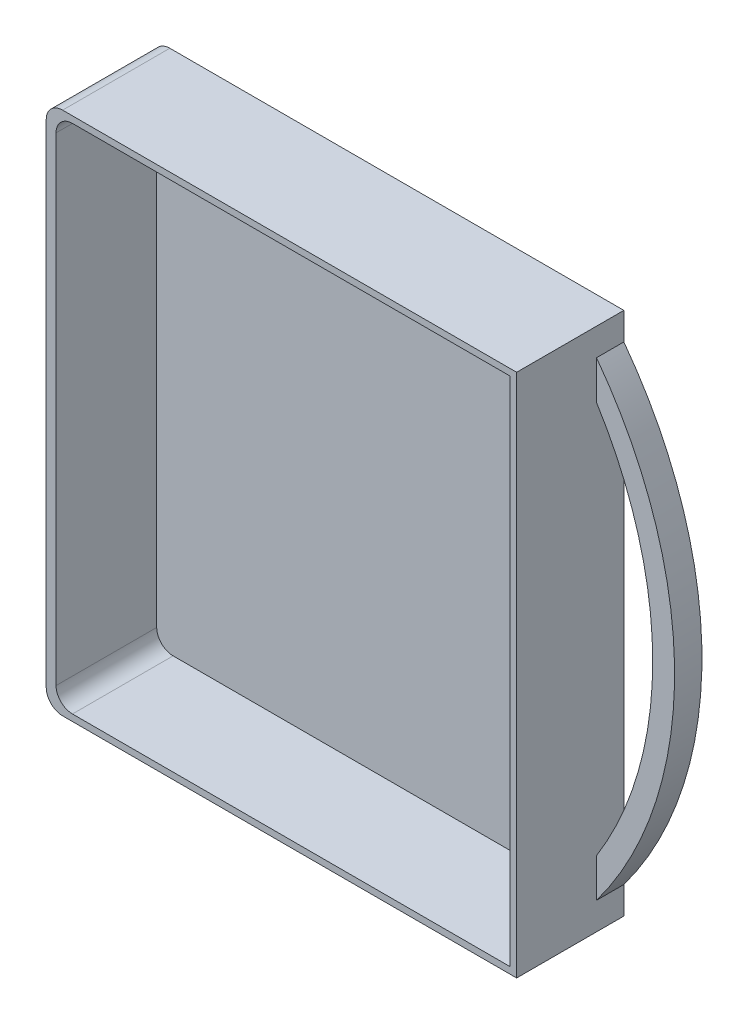
SolidWorks part; units mm, degrees
ref_plane "Спереди" through (0, 0, 0) normal (0, 0, 1) x (1, 0, 0)
ref_plane "Сверху" through (0, 0, 0) normal (0, 1, 0) x (1, 0, 0)
ref_plane "Справа" through (0, 0, 0) normal (1, 0, 0) x (0, 0, -1)
sketch "Эскиз1" plane through (0, 0, 0) normal (0, 0, 1) x (1, 0, 0)
  line L1 (-43, 47.95) -> (43, 47.95)
  line L2 (-43, 47.95) -> (-43, -47.95)
  line L3 (-43, -47.95) -> (43, -47.95)
  line L4 (43, 47.95) -> (43, -47.95)
  line L5 (-43, 47.95) -> (43, -47.95) construction
  line L6 (-43, -47.95) -> (43, 47.95) construction
  point P0 (0, 0)
  dimension "D1" = 86
  dimension "D2" = 95.9
extrude "Бобышка-Вытянуть1" add sketch "Эскиз1" along normal blind 19.6 separate body
sketch "Эскиз2" plane through (0, 0, 0) normal (0, 0, -1) x (-1, 0, 0)
  line L0 (-43, 35.8706) -> (-43, 42.95)
  line L1 (-43, -42.95) -> (-43, -35.8706)
  line L2 (-43, -47.95) -> (-43, 47.95) construction
  line L3 (-43, 47.95) -> (43, 47.95) construction
  line L4 (43, -47.95) -> (-43, -47.95) construction
  arc A0 (-43, 42.95) -> (-43, -42.95) centre (14.4749, 0) ccw
  arc A1 (-43, -35.8706) -> (-43, 35.8706) centre (14.4749, 0) cw
  point P5 (-53.2751, 0)
  point P12 (-43, 0)
  dimension "D1" = 67.75
  dimension "D3" = 5
  dimension "D4" = 5
  dimension "D2" = 4
  dimension "D5" = 10.2751
extrude "Бобышка-Вытянуть2" add sketch "Эскиз2" against normal blind 5
sketch "Эскиз3" plane through (0, 0, 19.6) normal (0, 0, 1) x (1, 0, 0)
  line L5 (-41.2, 47.95) -> (-41.2, -47.95)
  line L6 (-43, -46.75) -> (41.8, -46.75)
  line L7 (41.8, -46.75) -> (41.8, 46.75)
  line L8 (41.8, 46.75) -> (-43, 46.75)
  line L9 (-41.2, -46.75) -> (41.8, -46.75)
  line L10 (41.8, -46.75) -> (41.8, 46.75)
  line L11 (41.8, 46.75) -> (-41.2, 46.75)
  line L12 (-41.2, 46.75) -> (-41.2, -46.75)
  dimension "D1" = 1.2
  dimension "D2" = 1.8
extrude "Вырез-Вытянуть1" cut sketch "Эскиз3" against normal blind 18.4
fillet "Скругление1" radius 3 4 edges at (-41.2, 46.75, 10.4) (-41.2, -46.75, 10.4) (-43, -47.95, 9.8) (-43, 47.95, 9.8)
equation "\"D4@Эскиз2\"=\"D3@Эскиз2\""
